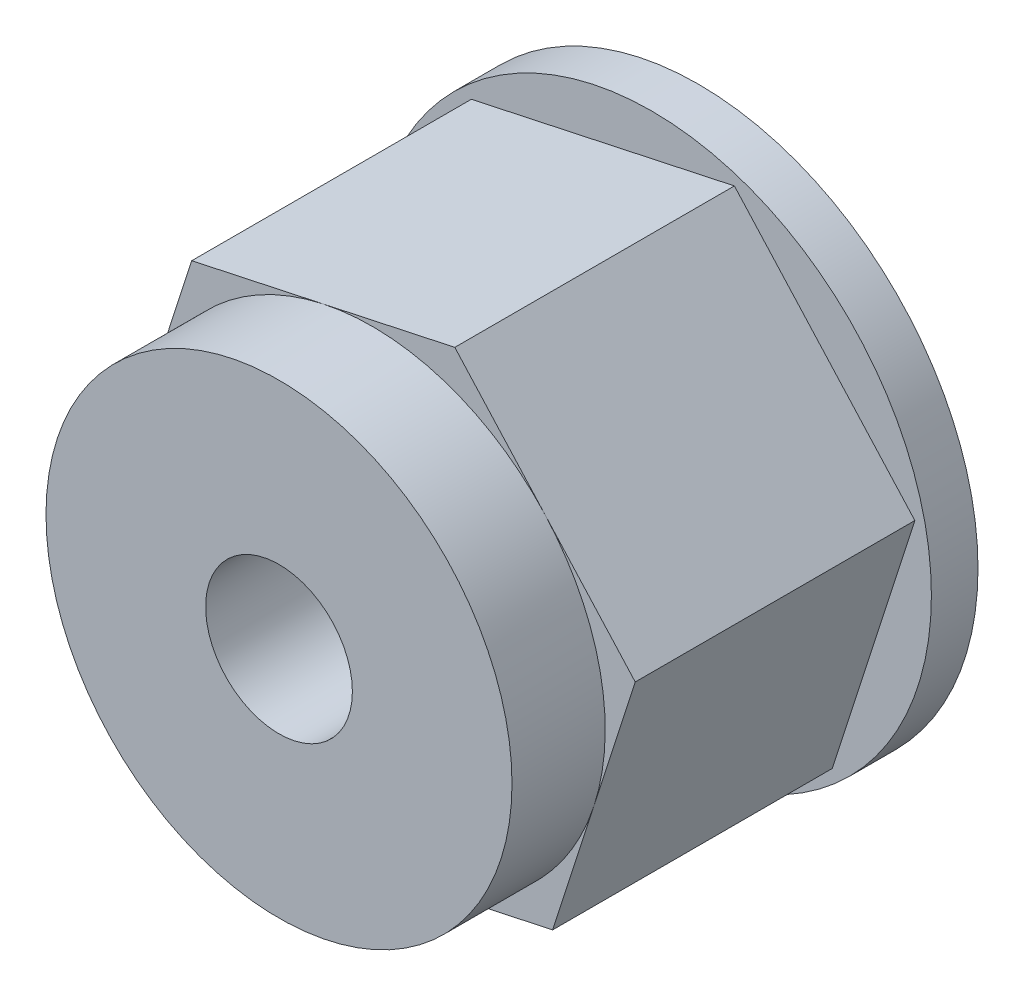
SolidWorks part; units mm, degrees
ref_plane "Front Plane" through (0, 0, 0) normal (0, 0, 1) x (1, 0, 0)
ref_plane "Top Plane" through (0, 0, 0) normal (0, 1, 0) x (1, 0, 0)
ref_plane "Right Plane" through (0, 0, 0) normal (1, 0, 0) x (0, 0, -1)
sketch "Sketch1" plane through (0, 0, 0) normal (0, 0, 1) x (1, 0, 0)
  circle A0 centre (0, 0) radius 7.62
  dimension "D1" = 15.24
extrude "Boss-Extrude1" add sketch "Sketch1" along normal blind 1.27
sketch "Sketch2" plane through (0, 0, 1.27) normal (0, 0, 1) x (1, 0, 0)
  line L1 (4.9176, -5.4388) -> (7.1689, 1.5394)
  line L2 (7.1689, 1.5394) -> (2.2513, 6.9782)
  line L3 (2.2513, 6.9782) -> (-4.9176, 5.4388)
  line L4 (-4.9176, 5.4388) -> (-7.1689, -1.5394)
  line L5 (-7.1689, -1.5394) -> (-2.2513, -6.9782)
  line L6 (-2.2513, -6.9782) -> (4.9176, -5.4388)
  circle A0 centre (0, 0) radius 6.35 construction
  dimension "D1" = 12.7
extrude "Boss-Extrude2" add sketch "Sketch2" along normal blind 7.62
sketch "Sketch4" plane through (0, 0, 8.89) normal (0, 0, 1) x (1, 0, 0)
  circle A0 centre (0, 0) radius 6.35
  dimension "D1" = 12.7
extrude "Boss-Extrude3" add sketch "Sketch4" along normal blind 2.54
sketch "Sketch5" plane through (0, 0, 11.43) normal (0, 0, 1) x (1, 0, 0)
  circle A0 centre (0, 0) radius 2
  dimension "D1" = 4
extrude "Cut-Extrude1" cut sketch "Sketch5" against normal through all and the other way through all contours A0
